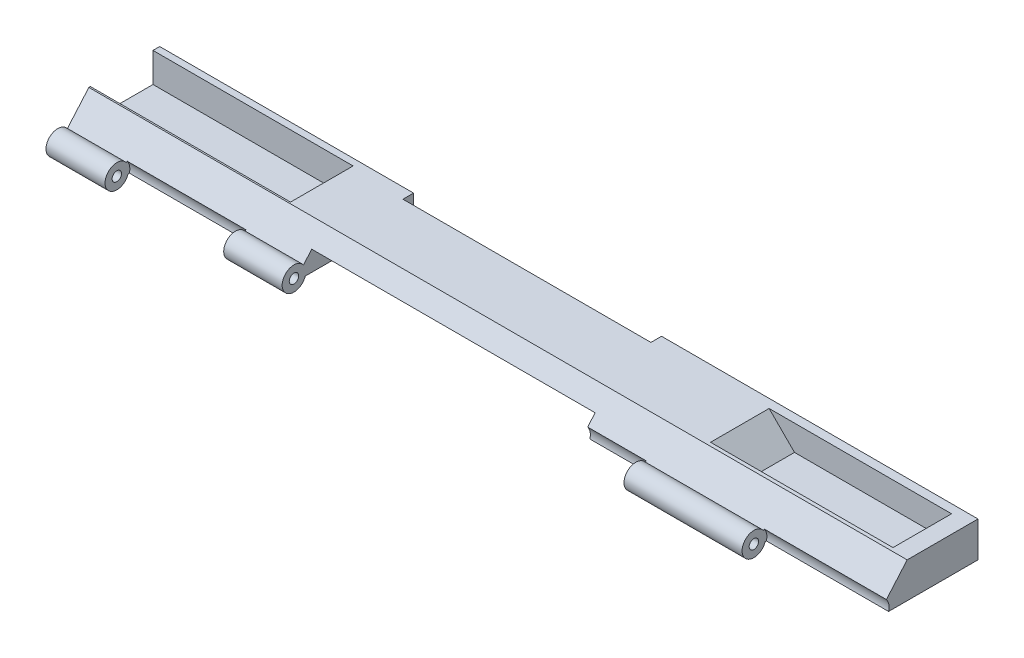
SolidWorks part; units mm, degrees
ref_plane "Front Plane" through (0, 0, 0) normal (0, 0, 1) x (1, 0, 0)
ref_plane "Top Plane" through (0, 0, 0) normal (0, 1, 0) x (1, 0, 0)
ref_plane "Right Plane" through (0, 0, 0) normal (1, 0, 0) x (0, 0, -1)
sketch "Sketch1" plane through (0, 0, 0) normal (1, 0, 0) x (0, 0, -1)
  line L5 (11.2654, -2.6366) -> (11.4585, -2.6366)
  line L6 (11.4585, -2.6366) -> (31.7785, -2.6366)
  line L7 (31.7785, -2.6366) -> (31.7785, 4.9834)
  line L8 (31.7785, 4.9834) -> (16.5385, 4.9834)
  line L9 (16.5385, 4.9834) -> (11.2654, -1.1126)
  circle A0 centre (9.8583, -1.8746) radius 0.8128
  circle A1 centre (9.8583, -1.8746) radius 1.6002
extrude "Boss-Extrude5" add sketch "Sketch1" along normal blind 162.56 contours A1 L5 L6 L7 L8 L9 | A1 A0
sketch "Sketch2" plane through (0, 0, -31.7785) normal (0, 0, -1) x (-1, 0, 0)
  line L0 (0, 4.9834) -> (0, -0.8586)
  line L1 (0, -2.6366) -> (0, 4.9834) construction
  line L2 (0, -0.8586) -> (-17.78, -0.8586)
  line L3 (-17.78, -0.8586) -> (-23.622, 4.9834)
  line L4 (-162.56, 4.9834) -> (0, 4.9834) construction
  line L5 (-23.622, 4.9834) -> (0, 4.9834)
extrude "Cut-Extrude1" cut sketch "Sketch2" against normal blind 14.351
sketch "Sketch3" plane through (0, 0, 0) normal (-1, 0, 0) x (0, 0, 1)
  line L0 (-31.7785, -0.8586) -> (-31.7785, 4.9834)
  line L1 (-31.7785, 4.9834) -> (-30.8895, 4.9834)
  line L2 (-17.4275, 4.9834) -> (-31.7785, 4.9834) construction
  line L3 (-30.8895, 4.9834) -> (-30.8895, -0.8586)
  line L4 (-17.4275, -0.8586) -> (-31.7785, -0.8586) construction
  line L5 (-30.8895, -0.8586) -> (-31.7785, -0.8586)
extrude "Boss-Extrude6" add sketch "Sketch3" against normal blind 36.957
sketch "Sketch7" plane through (0, 0, -31.7785) normal (0, 0, -1) x (-1, 0, 0)
  line L0 (-162.56, 4.9834) -> (-162.56, -0.4776)
  line L1 (-162.56, -2.6366) -> (-162.56, 4.9834) construction
  line L2 (-162.56, -0.4776) -> (-142.24, -0.4776)
  line L6 (-142.24, -0.4776) -> (-136.779, 4.9834)
  line L7 (-162.56, 4.9834) -> (0, 4.9834) construction
  line L8 (-136.779, 4.9834) -> (-162.56, 4.9834)
sketch "Sketch10" plane through (0, 0, -31.7785) normal (0, 0, -1) x (-1, 0, 0)
  line L0 (-162.56, -0.4776) -> (-142.24, -0.4776)
  line L1 (-142.24, -0.4776) -> (-136.779, 4.9834)
  line L2 (-136.779, 4.9834) -> (-162.56, 4.9834)
  line L3 (-162.56, 4.9834) -> (-162.56, -0.4776)
sketch "Sketch16" plane through (0, 0, 0) normal (-1, 0, 0) x (0, 0, 1)
  line L0 (-30.8895, 4.9834) -> (-17.4275, 4.9834)
  line L1 (-17.4275, 4.9834) -> (-17.4275, -1.4767)
  line L2 (-17.4275, -1.4767) -> (-30.8895, -1.4767)
  line L3 (-30.8895, -1.4767) -> (-30.8895, 4.9834)
extrude "Boss-Extrude7" add sketch "Sketch16" against normal blind 33.02
sketch "Sketch17" plane through (0, 0, -31.7785) normal (0, 0, -1) x (-1, 0, 0)
  line L0 (0, 4.9834) -> (0, -0.8586)
  line L1 (0, -2.6366) -> (0, 4.9834) construction
  line L2 (0, -0.8586) -> (-17.78, -0.8586)
  line L3 (-17.78, -0.8586) -> (-23.622, 4.9834)
  line L4 (-162.56, 4.9834) -> (0, 4.9834) construction
  line L5 (-23.622, 4.9834) -> (0, 4.9834)
extrude "Cut-Extrude4" cut sketch "Sketch17" against normal blind 15.24
sketch "Sketch18" plane through (0, 0, 0) normal (-1, 0, 0) x (0, 0, 1)
  line L0 (-31.7785, -0.8586) -> (-31.7785, 4.9834)
  line L1 (-31.7785, 4.9834) -> (-30.0005, 4.9834)
  line L2 (-16.5385, 4.9834) -> (-31.7785, 4.9834) construction
  line L3 (-30.0005, 4.9834) -> (-30.0005, -0.8586)
  line L4 (-16.5385, -0.8586) -> (-31.7785, -0.8586) construction
  line L5 (-30.0005, -0.8586) -> (-31.7785, -0.8586)
extrude "Boss-Extrude8" add sketch "Sketch18" against normal blind 38.1
sketch "Sketch19" plane through (0, 0, -31.7785) normal (0, 0, -1) x (-1, 0, 0)
  line L0 (-162.56, 4.9834) -> (-162.56, -0.4776)
  line L1 (-162.56, -0.4776) -> (-142.24, -0.4776)
  line L2 (-142.24, -0.4776) -> (-136.779, 4.9834)
  line L3 (-136.779, 4.9834) -> (-162.56, 4.9834)
extrude "Cut-Extrude5" cut sketch "Sketch19" against normal blind 14.224
sketch "Sketch20" plane through (162.56, 0, 0) normal (1, 0, 0) x (0, 0, -1)
  line L0 (31.7785, -0.4776) -> (31.7785, 4.9834)
  line L1 (31.7785, 4.9834) -> (29.6449, 4.9834)
  line L2 (17.5545, 4.9834) -> (31.7785, 4.9834) construction
  line L3 (29.6449, 4.9834) -> (29.6449, -0.4776)
  line L4 (17.5545, -0.4776) -> (31.7785, -0.4776) construction
  line L5 (29.6449, -0.4776) -> (31.7785, -0.4776)
extrude "Boss-Extrude9" add sketch "Sketch20" against normal blind 36.322
sketch "Sketch22" plane through (0, -0.4776, 0) normal (0, 1, 0) x (1, 0, 0)
  line L0 (157.2171, 21.9741) -> (145.9484, 21.9741)
  line L2 (157.2171, 19.1293) -> (145.9484, 19.1293)
  line L3 (145.9484, 25.1491) -> (157.2171, 25.1491)
  line L4 (145.9484, 27.9939) -> (157.2171, 27.9939)
  circle A0 centre (145.9484, 26.5715) radius 1.4224
  circle A1 centre (145.9484, 20.5517) radius 1.4224
  circle A2 centre (157.2171, 26.5715) radius 1.4224
  circle A3 centre (157.2171, 20.5517) radius 1.4224
extrude "Cut-Extrude7" cut sketch "Sketch22" against normal blind 24.13 and the other way blind 20.32 contours A0 | A2 L4 A0 L3 | A2 | A3 L0 A1 L2 | A3 | A1
sketch "Sketch25" plane through (0, 4.9834, 0) normal (0, 1, 0) x (1, 0, 0)
  line L0 (0, 11.2654) -> (0, 8.2581)
  line L1 (0, 8.2581) -> (25.146, 8.2581)
  line L2 (0, 8.2581) -> (162.56, 8.2581) construction
  line L3 (162.56, 8.2581) -> (137.414, 8.2581)
  line L4 (162.56, 8.2581) -> (162.56, 11.2654) construction
  line L5 (137.414, 8.2581) -> (137.414, 11.2654)
  line L6 (162.56, 11.2654) -> (0, 11.2654) construction
  line L7 (137.414, 11.2654) -> (25.146, 11.2654)
  line L8 (25.146, 11.2654) -> (25.146, 8.2581)
  line L9 (25.146, 8.2581) -> (137.414, 8.2581)
extrude "Cut-Extrude8" cut sketch "Sketch25" against normal blind 24.13 contours L8 L9 L5 L7
sketch "Sketch27" plane through (137.414, 0, 0) normal (-1, 0, 0) x (0, 0, 1)
  circle A0 centre (-9.8583, -1.8746) radius 1.778
extrude "Cut-Extrude9" cut sketch "Sketch27" along normal blind 112.268
sketch "Sketch31" plane through (0, 0, -31.7785) normal (0, 0, -1) x (-1, 0, 0)
  line L0 (-162.56, 4.9834) -> (-162.56, -0.4776)
  line L1 (-162.56, -2.6366) -> (-162.56, 4.9834) construction
  line L2 (-162.56, -0.4776) -> (-124.968, -0.4776)
  line L4 (-162.56, 4.9834) -> (0, 4.9834) construction
  line L5 (-124.079, 4.9834) -> (-162.56, 4.9834)
  line L6 (-124.968, -0.4776) -> (-119.507, 4.9834)
  line L7 (-119.507, 4.9834) -> (-124.079, 4.9834)
extrude "Cut-Extrude12" cut sketch "Sketch31" against normal blind 14.224
sketch "Sketch34" plane through (0, 4.9834, 0) normal (0, 1, 0) x (1, 0, 0)
  line L0 (119.507, 31.7785) -> (162.56, 31.7785)
  line L1 (162.56, 31.7785) -> (162.56, 29.6449)
  line L2 (162.56, 17.5545) -> (162.56, 31.7785) construction
  line L3 (162.56, 29.6449) -> (119.507, 29.6449)
  line L4 (119.507, 17.5545) -> (119.507, 31.7785) construction
  line L5 (119.507, 29.6449) -> (119.507, 31.7785)
extrude "Boss-Extrude14" add sketch "Sketch34" against normal blind 7.112
sketch "Sketch35" plane through (0, -0.4776, 0) normal (0, 1, 0) x (1, 0, 0)
  line L0 (162.56, 23.5997) -> (130.048, 23.5997)
  line L1 (162.56, 17.5545) -> (162.56, 29.6449) construction
  line L2 (145.9484, 25.1491) -> (130.048, 25.1491)
  line L3 (145.9484, 27.9939) -> (130.048, 27.9939)
  line L5 (145.9484, 21.9741) -> (130.048, 21.9741)
  line L6 (145.9484, 19.1293) -> (130.048, 19.1293)
  circle A0 centre (130.048, 26.5715) radius 1.4224
  circle A1 centre (130.048, 20.5517) radius 1.4224
  arc M2 (145.9484, 25.1491) -> (145.9484, 27.9939) centre (145.9484, 26.5715) cw
  arc M12 (145.9484, 19.1293) -> (145.9484, 21.9741) centre (145.9484, 20.5517) cw
extrude "Cut-Extrude13" cut sketch "Sketch35" against normal blind 7.112 contours A0 L2 L3 M2 | A1 L6 L5 M12 | A1 | A0
sketch "Sketch37" plane through (0, -2.6366, 0) normal (0, -1, 0) x (-1, 0, 0)
  line L3 (-111.76, 29.2385) -> (-111.76, 13.9985)
  line L4 (-111.76, 13.9985) -> (-50.8, 13.9985)
  line L5 (-50.8, 13.9985) -> (-50.8, 29.2385)
  line L6 (-50.8, 29.2385) -> (-111.76, 29.2385)
extrude "Cut-Extrude14" cut sketch "Sketch37" against normal blind 3.048
sketch "Sketch38" plane through (111.76, 0, 0) normal (-1, 0, 0) x (0, 0, 1)
  line L0 (-29.2385, -1.1126) -> (-27.9685, -1.1126)
  line L1 (-29.2385, 0.4114) -> (-29.2385, -2.6366) construction
  circle A0 centre (-27.9685, -1.1126) radius 0.8128
extrude "Cut-Extrude15" cut sketch "Sketch38" against normal blind 5.08
sketch "Sketch39" plane through (50.8, 0, 0) normal (1, 0, 0) x (0, 0, -1)
  line L0 (29.2385, -1.1126) -> (27.9685, -1.1126)
  line L1 (29.2385, 0.4114) -> (29.2385, -2.6366) construction
  circle A0 centre (27.9685, -1.1126) radius 0.8128
extrude "Cut-Extrude16" cut sketch "Sketch39" against normal blind 5.08
sketch "Sketch40" plane through (0, -2.6366, 0) normal (0, -1, 0) x (-1, 0, 0)
  line L0 (-111.76, 29.2385) -> (-111.76, 31.7785)
  line L1 (-162.56, 31.7785) -> (0, 31.7785) construction
  line L2 (-111.76, 31.7785) -> (-50.8, 31.7785)
  line L3 (-50.8, 31.7785) -> (-50.8, 29.2385)
  line L4 (-50.8, 29.2385) -> (-111.76, 29.2385)
extrude "Cut-Extrude17" cut sketch "Sketch40" against normal blind 3.048
sketch "Sketch41" plane through (50.8, 0, 0) normal (1, 0, 0) x (0, 0, -1)
  circle A0 centre (27.9685, -1.1126) radius 1.1613
extrude "Boss-Extrude15" add sketch "Sketch41" against normal blind 6.604
sketch "Sketch42" plane through (111.76, 0, 0) normal (-1, 0, 0) x (0, 0, 1)
  circle A0 centre (-27.9685, -1.1126) radius 1.0208
extrude "Boss-Extrude16" add sketch "Sketch42" against normal blind 5.588
sketch "Sketch43" plane through (50.8, 0, 0) normal (1, 0, 0) x (0, 0, -1)
  line L0 (31.7785, -1.1126) -> (30.5085, -1.1126)
  line L1 (31.7785, 0.4114) -> (31.7785, -2.6366) construction
  circle A0 centre (30.5085, -1.1126) radius 0.8128
extrude "Cut-Extrude18" cut sketch "Sketch43" against normal blind 5.08
sketch "Sketch44" plane through (111.76, 0, 0) normal (-1, 0, 0) x (0, 0, 1)
  line L0 (-31.7785, -1.1126) -> (-30.5085, -1.1126)
  line L1 (-31.7785, 0.4114) -> (-31.7785, -2.6366) construction
  circle A0 centre (-30.5085, -1.1126) radius 0.8128
extrude "Cut-Extrude19" cut sketch "Sketch44" against normal blind 5.08
sketch "Sketch46" plane through (0, -2.6366, 0) normal (0, -1, 0) x (-1, 0, 0)
  line L0 (-111.76, 13.9985) -> (-111.76, 4.9105)
  line L1 (-111.76, 4.9105) -> (-50.8, 4.9105)
  line L2 (-50.8, 4.9105) -> (-50.8, 13.9985)
  line L3 (-50.8, 13.9985) -> (-111.76, 13.9985)
extrude "Cut-Extrude21" cut sketch "Sketch46" against normal blind 3.048
sketch "Sketch47" plane through (0, 0.4114, 0) normal (0, -1, 0) x (-1, 0, 0)
  line L0 (-50.8, 31.7785) -> (-50.8, 29.4925)
  line L1 (-50.8, 11.4647) -> (-50.8, 31.7785) construction
  line L2 (-50.8, 29.4925) -> (-54.61, 29.4925)
  line L3 (-54.61, 29.4925) -> (-54.61, 31.7785)
  line L4 (-50.8, 31.7785) -> (-111.76, 31.7785) construction
  line L5 (-54.61, 31.7785) -> (-107.95, 31.7785)
  line L6 (-107.95, 31.7785) -> (-107.95, 29.4925)
  line L7 (-107.95, 29.4925) -> (-54.61, 29.4925)
  line M5 (-50.8, 31.7785) -> (-111.76, 31.7785)
extrude "Cut-Extrude22" cut sketch "Sketch47" against normal blind 15.24 contours L6 L7 L3 M5
sketch "Sketch48" plane through (0, 0, 0) normal (-1, 0, 0) x (0, 0, 1)
  circle A0 centre (-9.8583, -1.8746) radius 2.54
extrude "Boss-Extrude17" add sketch "Sketch48" against normal blind 25.146
sketch "Sketch49" plane through (162.56, 0, 0) normal (1, 0, 0) x (0, 0, -1)
  circle A0 centre (9.8583, -1.8746) radius 2.54
extrude "Boss-Extrude18" add sketch "Sketch49" against normal blind 25.146
sketch "Sketch50" plane through (137.414, 0, 0) normal (-1, 0, 0) x (0, 0, 1)
  circle A0 centre (-9.8583, -1.8746) radius 2.794
extrude "Cut-Extrude23" cut sketch "Sketch50" along normal blind 112.268
sketch "Sketch51" plane through (162.56, 0, 0) normal (1, 0, 0) x (0, 0, -1)
  circle A0 centre (9.8583, -1.8746) radius 1.27
extrude "Cut-Extrude24" cut sketch "Sketch51" against normal blind 174.498
sketch "Sketch52" plane through (0, 0.4114, 0) normal (0, -1, 0) x (-1, 0, 0)
  line L0 (-50.8, 31.7785) -> (-50.8, 12.5464)
  line L1 (-50.8, 12.5464) -> (-111.76, 12.6523)
  line L2 (-111.76, 12.6523) -> (-111.76, 31.7785)
  line L3 (-111.76, 31.7785) -> (-50.8, 31.7785)
extrude "Cut-Extrude25" cut sketch "Sketch52" against normal blind 1.27
ref_plane "Plane1" through (72.2732, 0.4114, -12.5837) normal (-1, 0, 0) x (0, 0, 1)
sketch "Sketch55" plane through (0, -2.6366, 0) normal (0, -1, 0) x (1, 0, 0)
  line L0 (111.76, -13.6822) -> (111.76, -7.8087)
  line L1 (111.76, -7.8087) -> (65.0565, -7.8087)
  line L2 (65.0565, -7.8087) -> (65.0565, -13.6822)
  line L3 (50.8, -13.6822) -> (111.76, -13.6822) construction
  line L4 (65.0565, -13.6822) -> (111.76, -13.6822)
extrude "Cut-Extrude26" cut sketch "Sketch55" against normal blind 8.636 and the other way blind 9.144
sketch "Sketch57" plane through (45.72, 0, 0) normal (1, 0, 0) x (0, 0, -1)
  circle A0 centre (30.5085, -1.1126) radius 1.0293
extrude "Boss-Extrude20" add sketch "Sketch57" along normal blind 5.08
sketch "Sketch58" plane through (111.76, 0, 0) normal (-1, 0, 0) x (0, 0, 1)
  circle A0 centre (-30.5085, -1.1126) radius 1.0927
extrude "Boss-Extrude21" add sketch "Sketch58" against normal blind 7.112
sketch "Sketch59" plane through (50.8, 0, 0) normal (1, 0, 0) x (0, 0, -1)
  line L0 (31.7785, -0.4776) -> (29.2385, -0.4776)
  line L1 (31.7785, 1.6814) -> (31.7785, -2.6366) construction
  circle A0 centre (29.2385, -0.4776) radius 1.016
extrude "Cut-Extrude27" cut sketch "Sketch59" against normal blind 5.08 and the other way blind 66.04
sketch "Sketch60" plane through (0, 0, 0) normal (-1, 0, 0) x (0, 0, 1)
  circle A0 centre (-9.8583, -1.8746) radius 1.016
  circle A1 centre (-9.8583, -1.8746) radius 1.8695
extrude "Boss-Extrude22" add sketch "Sketch60" against normal blind 162.56
sketch "Sketch61" plane through (137.414, 0, 0) normal (-1, 0, 0) x (0, 0, 1)
  circle A0 centre (-9.8583, -1.8746) radius 2.2194
extrude "Cut-Extrude28" cut sketch "Sketch61" along normal blind 112.268
sketch "Sketch62" plane through (25.146, 0, 0) normal (1, 0, 0) x (0, 0, -1)
  line L0 (11.9061, -0.3719) -> (12.4252, 0.2282)
  line L1 (12.2813, -2.6366) -> (12.6983, -2.6366)
  line L2 (12.6983, -2.6366) -> (12.8765, -1.4304)
  line L3 (12.4252, 0.2282) -> (12.8765, -1.4304)
  circle A0 centre (9.8583, -1.8746) radius 2.54
  circle A1 centre (9.8583, -1.8746) radius 1.016
  arc M1 (11.9061, -0.3719) -> (12.2813, -2.6366) centre (9.8583, -1.8746) ccw
  line M2 (12.2813, -2.6366) -> (12.5464, -2.6366)
  arc M3 (12.5464, -2.6366) -> (12.0761, -0.1753) centre (9.8583, -1.8746) ccw
  line M4 (12.0761, -0.1753) -> (11.9061, -0.3719)
  circle M5 centre (9.8583, -1.8746) radius 1.016
extrude "Boss-Extrude26" add sketch "Sketch62" along normal blind 25.654 contours A0 M2 M3 M4 | A0 M1 M5
sketch "Sketch65" plane through (137.414, 0, 0) normal (-1, 0, 0) x (0, 0, 1)
  line L0 (-11.9061, -0.3719) -> (-12.3768, 0.1722)
  line L1 (-12.2813, -2.6366) -> (-13.0464, -2.6366)
  line L2 (-13.0464, -2.6366) -> (-13.0464, -0.8123)
  line L3 (-13.0464, -0.8123) -> (-12.3768, 0.1722)
  circle A0 centre (-9.8583, -1.8746) radius 2.54
  circle A1 centre (-9.8583, -1.8746) radius 1.016
  line M1 (-12.5464, -2.6366) -> (-12.2813, -2.6366)
  arc M2 (-12.2813, -2.6366) -> (-11.9061, -0.3719) centre (-9.8583, -1.8746) ccw
  line M3 (-11.9061, -0.3719) -> (-12.0761, -0.1753)
  arc M4 (-12.0761, -0.1753) -> (-12.5464, -2.6366) centre (-9.8583, -1.8746) ccw
  circle M5 centre (-9.8583, -1.8746) radius 1.016
extrude "Boss-Extrude27" add sketch "Sketch65" along normal blind 25.654 contours A0 M3 M4 M1 | A0 M2 M5
sketch "Sketch67" plane through (162.56, 0, 0) normal (1, 0, 0) x (0, 0, -1)
  circle A0 centre (9.8583, -1.8746) radius 2.794
extrude "Cut-Extrude32" cut sketch "Sketch67" against normal blind 12.827
sketch "Sketch68" plane through (111.76, 0, 0) normal (-1, 0, 0) x (0, 0, 1)
  circle A0 centre (-9.8583, -1.8746) radius 2.794
extrude "Cut-Extrude33" cut sketch "Sketch68" against normal blind 12.827
sketch "Sketch70" plane through (0, -6.0502, -6.9944) normal (0, 0.6542, 0.7563) x (1, 0, 0)
  line L0 (0, 7.5078) -> (12.573, 7.5078)
  line L1 (0, 7.5078) -> (50.8, 7.5078) construction
ref_plane "Plane2" through (12.573, 0, 0) normal (-1, 0, 0) x (0, 0, 1)
sketch "Sketch72" plane through (12.573, 0, 0) normal (-1, 0, 0) x (0, 0, 1)
  circle A0 centre (-9.8583, -1.8746) radius 2.794
extrude "Cut-Extrude34" cut sketch "Sketch72" against normal blind 25.654
sketch "Sketch74" plane through (12.573, 0, 0) normal (-1, 0, 0) x (0, 0, 1)
  line L0 (-12.2813, -2.6366) -> (-13.0347, -2.6366)
  line L1 (-12.5464, -2.6366) -> (-31.7785, -2.6366) construction
  line L2 (-13.0347, -2.6366) -> (-13.4092, -1.2331)
  line L3 (-13.4092, -1.2331) -> (-12.2813, 0.0618)
  line L4 (-16.5385, 4.9834) -> (-12.0761, -0.1753) construction
  line L5 (-12.2813, 0.0618) -> (-11.9061, -0.3719)
  circle A0 centre (-9.8583, -1.8746) radius 2.54
  circle A1 centre (-9.8583, -1.8746) radius 1.016
extrude "Boss-Extrude28" add sketch "Sketch74" against normal blind 0.127 contours A0 A1 | A0 L5 L3 L2 L0
sketch "Sketch77" plane through (124.587, 0, 0) normal (-1, 0, 0) x (0, 0, 1)
  line L0 (-12.2813, -2.6366) -> (-13.3172, -2.6366)
  line L1 (-12.5464, -2.6366) -> (-31.7785, -2.6366) construction
  line L2 (-13.3172, -2.6366) -> (-13.5466, -0.8586)
  line L3 (-13.5466, -0.8586) -> (-12.4857, 0.2981)
  line L4 (-16.5385, 4.9834) -> (-12.0761, -0.1753) construction
  line L5 (-12.4857, 0.2981) -> (-11.9061, -0.3719)
  circle A0 centre (-9.8583, -1.8746) radius 2.54
  circle A1 centre (-9.8583, -1.8746) radius 1.016
  line M1 (-11.9061, -0.3719) -> (-12.0761, -0.1753)
  arc M2 (-12.0761, -0.1753) -> (-12.5464, -2.6366) centre (-9.8583, -1.8746) ccw
  line M3 (-12.5464, -2.6366) -> (-12.2813, -2.6366)
  arc M4 (-12.2813, -2.6366) -> (-11.9061, -0.3719) centre (-9.8583, -1.8746) ccw
  circle M5 centre (-9.8583, -1.8746) radius 1.016
extrude "Boss-Extrude29" add sketch "Sketch77" along normal blind 0.254 contours A0 M4 M5 | A0 M1 M2 M3
sketch "Sketch79" plane through (0, 0, 0) normal (-1, 0, 0) x (0, 0, 1)
  circle A0 centre (-9.8583, -1.8746) radius 1.016
extrude "Cut-Extrude35" cut sketch "Sketch79" against normal blind 15.748
sketch "Sketch87" plane through (0, 4.9834, 0) normal (0, 1, 0) x (1, 0, 0)
  line L0 (23.622, 30.0005) -> (23.622, 16.5385)
  line L1 (23.622, 16.5385) -> (0, 16.5385)
  line L2 (0, 16.5385) -> (0, 30.0005)
  line L3 (0, 30.0005) -> (23.622, 30.0005)
extrude "Boss-Extrude30" add sketch "Sketch87" against normal blind 6.096
sketch "Sketch88" plane through (0, 0, -31.7785) normal (0, 0, -1) x (-1, 0, 0)
  line L0 (0, 4.9834) -> (0, -1.3666)
  line L1 (0, -2.6366) -> (0, 4.9834) construction
  line L2 (0, -1.3666) -> (-17.78, -1.3666)
  line L3 (0, 4.9834) -> (-23.622, 4.9834)
  line L4 (-54.61, 4.9834) -> (0, 4.9834) construction
  line L5 (-23.622, 4.9834) -> (-17.78, -1.3666)
extrude "Cut-Extrude36" cut sketch "Sketch88" against normal blind 14.9098
sketch "Sketch89" plane through (0, 0, 0) normal (-1, 0, 0) x (0, 0, 1)
  line L0 (-31.7785, -1.3666) -> (-31.7785, 4.9834)
  line L1 (-31.7785, 4.9834) -> (-30.3307, 4.9834)
  line L2 (-16.8687, 4.9834) -> (-31.7785, 4.9834) construction
  line L3 (-30.3307, 4.9834) -> (-30.3307, -1.3666)
  line L4 (-16.8687, -1.3666) -> (-31.7785, -1.3666) construction
  line L5 (-30.3307, -1.3666) -> (-31.7785, -1.3666)
extrude "Boss-Extrude31" add sketch "Sketch89" against normal blind 30.6578
sketch "Sketch92" plane through (162.56, 0, 0) normal (1, 0, 0) x (0, 0, -1)
  line L0 (29.6449, 4.9834) -> (29.6449, -2.6366)
  line L1 (12.5464, -2.6366) -> (31.7785, -2.6366) construction
  line L2 (29.6449, 4.9834) -> (17.5545, 4.9834)
  line L3 (17.5545, 4.9834) -> (17.5545, -2.6366)
  line L4 (17.5545, -2.6366) -> (29.6449, -2.6366)
extrude "Boss-Extrude33" add sketch "Sketch92" against normal blind 43.18
sketch "Sketch94" plane through (162.56, 0, 0) normal (1, 0, 0) x (0, 0, -1)
  line L0 (31.7785, 4.9834) -> (31.7785, -2.6366)
  line L1 (31.7785, -2.6366) -> (12.5464, -2.6366)
  line L2 (12.0761, -0.1753) -> (16.5385, 4.9834)
  line L3 (16.5385, 4.9834) -> (31.7785, 4.9834)
  circle A0 centre (9.8583, -1.8746) radius 2.794
  line M1 (12.5464, -2.6366) -> (31.7785, -2.6366)
  line M2 (31.7785, -2.6366) -> (31.7785, 4.9834)
  line M3 (31.7785, 4.9834) -> (16.5385, 4.9834)
  line M4 (16.5385, 4.9834) -> (12.0761, -0.1753)
  arc M5 (12.0761, -0.1753) -> (12.5464, -2.6366) centre (9.8583, -1.8746) cw
extrude "Boss-Extrude34" add sketch "Sketch94" along normal blind 13.462 contours M5 M1 M2 M3 M4
sketch "Sketch95" plane through (0, 0, 0) normal (-1, 0, 0) x (0, 0, 1)
  line L1 (-30.3307, -1.3666) -> (-16.8687, -1.3666)
  line L2 (-30.3307, -1.3666) -> (-30.3307, 4.9834)
  line L3 (-30.3307, 4.9834) -> (-16.8687, 4.9834)
  line L4 (-16.8687, -1.3666) -> (-16.8687, 4.9834)
extrude "Cut-Extrude37" cut sketch "Sketch95" against normal blind 43.053
sketch "Sketch96" plane through (0, 0, -31.7785) normal (0, 0, -1) x (-1, 0, 0)
  line L0 (0, 4.9834) -> (-43.053, 4.9834)
  line L1 (-54.61, 4.9834) -> (0, 4.9834) construction
  line L2 (-43.053, 4.9834) -> (-43.053, -2.2287)
  line L3 (-43.053, 4.9834) -> (-35.8409, -2.2287)
  line L4 (-35.8409, -2.2287) -> (-43.053, -2.2287)
extrude "Boss-Extrude35" add sketch "Sketch96" against normal blind 15.113 contours L4 L3 L2
sketch "Sketch97" plane through (176.022, 0, 0) normal (1, 0, 0) x (0, 0, -1)
  line L0 (17.3005, 4.9834) -> (17.3005, -0.4776)
  line L1 (31.7785, 4.9834) -> (16.5385, 4.9834) construction
  line L2 (17.3005, -0.4776) -> (29.8989, -0.4776)
  line L3 (29.8989, 4.9834) -> (17.3005, 4.9834)
  line L4 (29.8989, 4.9834) -> (29.8989, -0.4776)
extrude "Cut-Extrude38" cut sketch "Sketch97" against normal blind 43.053
sketch "Sketch98" plane through (0, 0, -31.7785) normal (0, 0, -1) x (-1, 0, 0)
  line L0 (-176.022, 4.9834) -> (-132.969, 4.9834)
  line L1 (-176.022, 4.9834) -> (-107.95, 4.9834) construction
  line L2 (-132.969, 4.9834) -> (-132.969, -1.9378)
  line L3 (-132.969, 4.9834) -> (-139.8902, -1.9378)
  line L4 (-139.8902, -1.9378) -> (-132.969, -1.9378)
extrude "Boss-Extrude36" add sketch "Sketch98" against normal blind 14.859 contours L3 L4 L2
sketch "Sketch99" plane through (176.022, 0, 0) normal (1, 0, 0) x (0, 0, -1)
  line L1 (17.3005, -0.4776) -> (29.8989, -0.4776)
  line L2 (17.3005, -0.4776) -> (17.3005, 4.9834)
  line L3 (17.3005, 4.9834) -> (29.8989, 4.9834)
  line L4 (29.8989, -0.4776) -> (29.8989, 4.9834)
extrude "Boss-Extrude37" add sketch "Sketch99" against normal blind 3.81
